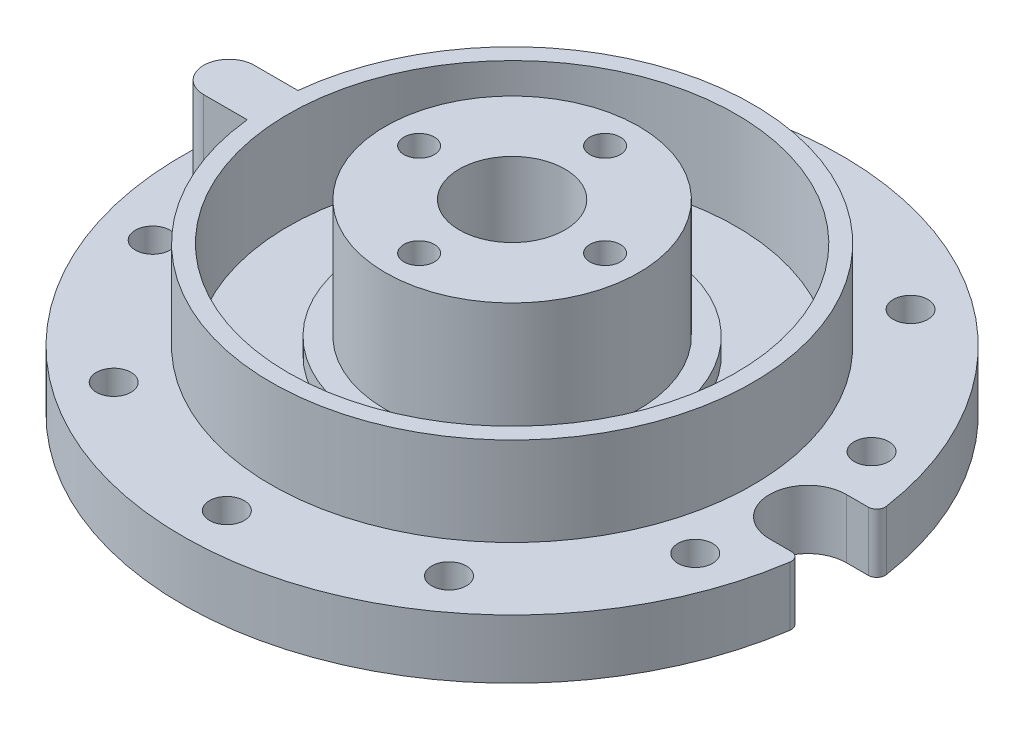
SolidWorks part; units mm, degrees
ref_plane "Front Plane" through (0, 0, 0) normal (0, 0, 1) x (1, 0, 0)
ref_plane "Top Plane" through (0, 0, 0) normal (0, 1, 0) x (1, 0, 0)
ref_plane "Right Plane" through (0, 0, 0) normal (1, 0, 0) x (0, 0, -1)
sketch "Sketch1" plane through (0, 0, 0) normal (0, 1, 0) x (1, 0, 0)
  circle A0 centre (0, 0) radius 39
  dimension "D1" = 78
extrude "Boss-Extrude1" add sketch "Sketch1" along normal blind 7
sketch "Sketch3" plane through (0, 7, 0) normal (0, 1, 0) x (1, 0, 0)
  circle A0 centre (0, 0) radius 17.5
  dimension "D1" = 35
extrude "Boss-Extrude2" add sketch "Sketch3" along normal blind 1
sketch "Sketch4" plane through (0, 8, 0) normal (0, 1, 0) x (1, 0, 0)
  circle A0 centre (0, 0) radius 15
  dimension "D1" = 30
extrude "Boss-Extrude3" add sketch "Sketch4" along normal blind 14 contours A0
sketch "Sketch5" plane through (0, 22, 0) normal (0, 1, 0) x (1, 0, 0)
  circle A0 centre (0, 0) radius 6.25
  circle A1 centre (0, 11) radius 1.8
  circle A2 centre (11, 0) radius 1.8
  circle A3 centre (0, -11) radius 1.8
  circle A4 centre (-11, 0) radius 1.8
  dimension "D1" = 12.5
  dimension "D3" = 3.6
  dimension "D2" = 11
  dimension "D4" = 4
extrude "Cut-Extrude1" cut sketch "Sketch5" against normal through all
hole_wizard "CSK for M4 Countersunk Flat Head Screw1" positions "3DSketch1" profile "Sketch6" countersink size "M4" standard "ISO" end condition through all
sketch3d "3DSketch1"
  line L0 (11, 0, 0) -> (11, 22, 0) construction
  line L1 (0, 0, -11) -> (0, 22, -11) construction
  line L2 (-11, 0, 0) -> (-11, 22, 0) construction
  line L3 (0, 0, 11) -> (0, 22, 11) construction
  point P0 (11, 0, 0)
  point P4 (0, 0, -11)
  point P8 (-11, 0, 0)
  point P12 (0, 0, 11)
sketch "Sketch6" plane through (11, 0, 0) normal (1, 0, 0) x (0, 0, -1)
  line L0 (0, 0) -> (0, 22)
  line L1 (0, 22) -> (1.75, 22)
  line L2 (1.75, 22) -> (1.75, 2.8)
  line L3 (1.75, 2.8) -> (4.55, 0)
  line L5 (4.55, 0) -> (0, 0)
  line L6 (-1.75, 2.8) -> (-4.55, 0) construction
  line L11 (0, -6.35) -> (0, 107.95) construction
  dimension "Thru Hole Dia." = 3.5
  dimension "Thru Hole Depth" = 22
  dimension "Near C'Sink Dia." = 9.1
  dimension "Near C'Sink Angle" = 90
sketch "Sketch7" plane through (0, 7, 0) normal (0, 1, 0) x (1, 0, 0)
  circle A0 centre (0, 0) radius 26.5
  circle A1 centre (0, 0) radius 28.5
  dimension "D1" = 53
  dimension "D2" = 2
extrude "Boss-Extrude4" add sketch "Sketch7" along normal blind 10.5
sketch "Sketch8" plane through (0, 7, 0) normal (0, 1, 0) x (1, 0, 0)
  circle A0 centre (0, 0) radius 17.5 construction
  circle A1 centre (0, 0) radius 26.5
  circle A2 centre (0, 0) radius 26.5
  circle A3 centre (0, 0) radius 17.5
  dimension "D1" = 0
extrude "Cut-Extrude2" cut sketch "Sketch8" against normal blind 1
sketch "Sketch9" plane through (0, 7, 0) normal (0, 1, 0) x (1, 0, 0)
  line L0 (0, 0) -> (0, 33.75) construction
  circle A0 centre (0, 33.75) radius 2.05
  circle A1 centre (19.8378, 27.3043) radius 2.05
  circle A2 centre (32.0982, 10.4293) radius 2.05
  circle A3 centre (32.0982, -10.4293) radius 2.05
  circle A4 centre (19.8378, -27.3043) radius 2.05
  circle A5 centre (0, -33.75) radius 2.05
  circle A6 centre (-19.8378, -27.3043) radius 2.05
  circle A7 centre (-32.0982, -10.4293) radius 2.05
  circle A8 centre (-32.0982, 10.4293) radius 2.05
  circle A9 centre (-19.8378, 27.3043) radius 2.05
  dimension "D2" = 4.1
  dimension "D1" = 33.75
  dimension "D3" = 10
extrude "Cut-Extrude3" cut sketch "Sketch9" against normal through all
sketch "Sketch10" plane through (0, 7, 0) normal (0, 1, 0) x (1, 0, 0)
  line L0 (-33.5, 0) -> (0, 0) construction
  line L1 (-33.5, 3) -> (-28.3417, 3)
  line L2 (-33.5, -3) -> (-28.3417, -3)
  arc A0 (-33.5, 3) -> (-33.5, -3) centre (-33.5, 0) ccw
  circle A1 centre (0, 0) radius 28.5 construction
  arc A2 (-28.3417, 3) -> (-28.3417, -3) centre (0, 0) ccw
  dimension "D2" = 6
  dimension "D1" = 33.5
extrude "Boss-Extrude5" add sketch "Sketch10" along normal up to surface (10.5 mm away) up to face at (0, 17.5, 28.5)
sketch "Sketch11" plane through (0, 7, 0) normal (0, 1, 0) x (1, 0, 0)
  line L0 (0, 0) -> (35, 0) construction
  line L1 (35, 4.55) -> (38.7337, 4.55)
  line L2 (35, -4.55) -> (38.7337, -4.55)
  arc A0 (35, 4.55) -> (35, -4.55) centre (35, 0) ccw
  circle A1 centre (0, 0) radius 39 construction
  arc A2 (38.7337, -4.55) -> (38.7337, 4.55) centre (0, 0) ccw
  dimension "D1" = 9.1
  dimension "D2" = 35
extrude "Cut-Extrude4" cut sketch "Sketch11" against normal through all contours L1 A2 L2 A0
fillet "Fillet1" radius 1 2 edges at (38.7337, 3.5, 4.55) (38.7337, 3.5, -4.55)
